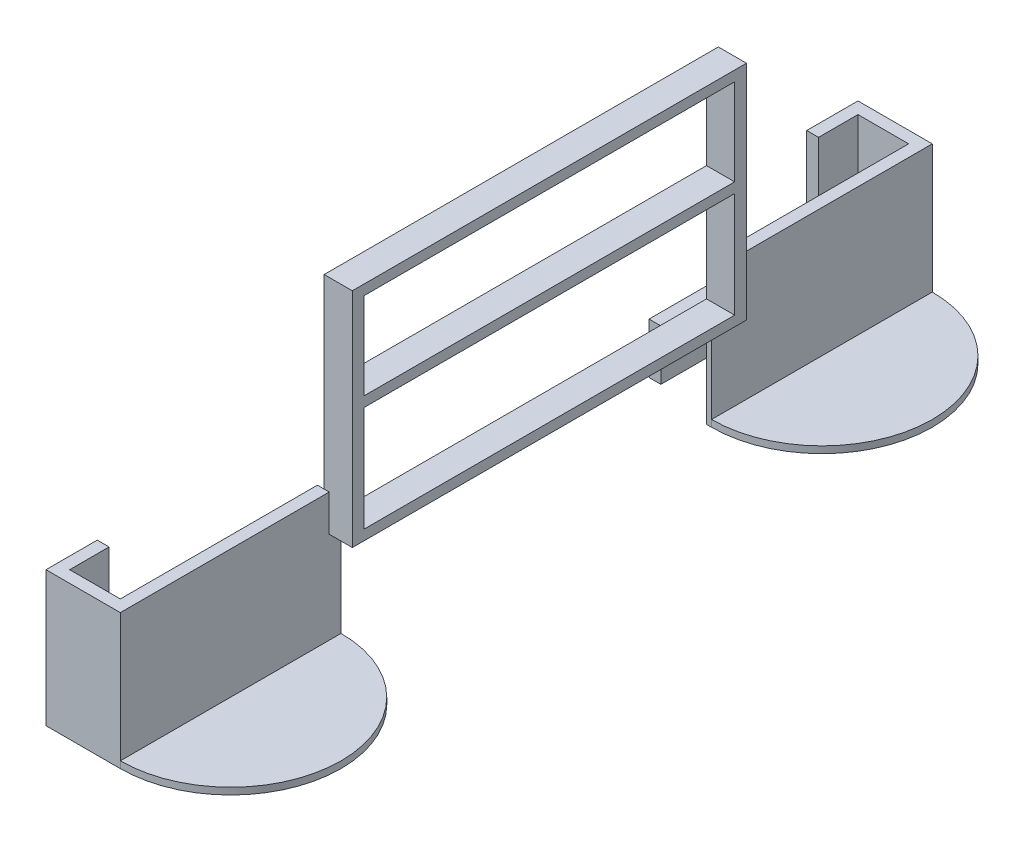
SolidWorks part; units mm, degrees
ref_plane "Alzado" through (0, 0, 0) normal (0, 0, 1) x (1, 0, 0)
ref_plane "Planta" through (0, 0, 0) normal (0, 1, 0) x (1, 0, 0)
ref_plane "Vista lateral" through (0, 0, 0) normal (1, 0, 0) x (0, 0, -1)
sketch "Croquis3" plane through (0, 0, 0) normal (0, 0, 1) x (1, 0, 0)
  line L0 (-207.2321, -11.9301) -> (-207.2321, -18.9301)
  line L1 (-207.2321, -11.9301) -> (-205.1321, -11.9301)
  line L2 (-205.1321, -11.9301) -> (-205.1321, -18.9301)
  line L3 (-205.1321, -18.9301) -> (-196.1321, -18.9301)
  line L4 (-196.1321, -18.9301) -> (-196.1321, -11.9301)
  line L5 (-196.1321, -11.9301) -> (-194.0321, -11.9301)
  line L6 (-194.0321, -11.9301) -> (-194.0321, -20.9301)
  line L7 (-194.0321, -20.9301) -> (-207.2321, -20.9301)
  line L8 (-207.2321, -20.9301) -> (-207.2321, -18.9301)
  dimension "D1" = 7
  dimension "D2" = 9
  dimension "D3" = 2.1
  dimension "D4" = 2.1
  dimension "D5" = 13.2
extrude "Saliente-Extruir2" add sketch "Croquis3" along normal blind 35
sketch "Croquis4" plane through (0, -18.9301, 0) normal (0, 1, 0) x (1, 0, 0)
  line L0 (-196.1321, -35) -> (-196.1321, 0) construction
  line L1 (-205.1321, 0) -> (-196.1321, 0)
  line L2 (-205.1321, 0) -> (-205.1321, -15)
  line L3 (-205.1321, -15) -> (-196.1321, -15)
  line L4 (-196.1321, 0) -> (-196.1321, -15)
  dimension "D1" = 15
extrude "Cortar-Extruir1" cut sketch "Croquis4" against normal blind 70
sketch "Croquis7" plane through (0, 0, 35) normal (0, 0, 1) x (1, 0, 0)
  line L0 (-205.1321, -11.9301) -> (-205.1321, 3.0699)
  line L1 (-205.1321, 3.0699) -> (-207.2321, 3.0699)
  line L2 (-207.2321, 3.0699) -> (-207.2321, -20.9301)
  line L3 (-207.2321, -20.9301) -> (-194.0321, -20.9301)
  line L4 (-194.0321, -20.9301) -> (-194.0321, 3.0699)
  line L5 (-194.0321, 3.0699) -> (-196.1321, 3.0699)
  line L9 (-196.1321, 3.0699) -> (-196.1321, -11.9301)
  line L10 (-196.1321, -11.9301) -> (-205.1321, -11.9301)
  dimension "D1" = 15
extrude "Saliente-Extruir3" add sketch "Croquis7" along normal blind 2.1
sketch "Croquis8" plane through (0, 0, 35) normal (0, 0, -1) x (-1, 0, 0)
  line L1 (194.0321, 3.0699) -> (196.1321, 3.0699)
  line L2 (194.0321, 3.0699) -> (194.0321, -11.9301)
  line L3 (194.0321, -11.9301) -> (196.1321, -11.9301)
  line L4 (196.1321, 3.0699) -> (196.1321, -11.9301)
  line L5 (205.1321, 3.0699) -> (207.2321, 3.0699)
  line L6 (205.1321, 3.0699) -> (205.1321, -11.9301)
  line L7 (205.1321, -11.9301) -> (207.2321, -11.9301)
  line L8 (207.2321, 3.0699) -> (207.2321, -11.9301)
extrude "Saliente-Extruir4" add sketch "Croquis8" along normal blind 7
sketch "Croquis9" plane through (-194.0321, 0, 0) normal (1, 0, 0) x (0, 0, -1)
  line L1 (-28, 3.0699) -> (0, 3.0699)
  line L2 (-28, 3.0699) -> (-28, -11.9301)
  line L3 (-28, -11.9301) -> (0, -11.9301)
  line L4 (0, 3.0699) -> (0, -11.9301)
extrude "Saliente-Extruir5" add sketch "Croquis9" against normal up to vertex
sketch "Croquis10" plane through (0, 0, 37.1) normal (0, 0, 1) x (1, 0, 0)
  line L1 (-205.1321, 3.0699) -> (-196.1321, 3.0699)
  line L2 (-205.1321, 3.0699) -> (-205.1321, -11.9301)
  line L3 (-205.1321, -11.9301) -> (-196.1321, -11.9301)
  line L4 (-196.1321, 3.0699) -> (-196.1321, -11.9301)
extrude "Saliente-Extruir6" add sketch "Croquis10" against normal up to vertex
sketch "Croquis11" plane through (-196.1321, 0, 0) normal (-1, 0, 0) x (0, 0, 1)
  line L0 (35, 3.0699) -> (35, -18.9301) construction
  line L2 (-35, -7.9301) -> (-35, -27.9301) construction
  dimension "D1" = 70
ref_plane "Plano1" through (0, 0, -35) normal (0, 0, -1) x (-1, 0, 0)
sketch "Croquis12" plane through (-194.0321, 0, 0) normal (1, 0, 0) x (0, 0, -1)
  line L0 (0, 3.0699) -> (0, 36.0699)
  line L1 (0, 36.0699) -> (35, 36.0699)
  line L2 (-37.1, -20.9301) -> (-37.1, 3.0699) construction
  line L3 (0, -20.9301) -> (2.1, -20.9301)
  line L4 (2.1, -20.9301) -> (2.1, -3.4301)
  line L5 (2.1, -3.4301) -> (35, -3.4301)
  line L6 (2.1, -1.6301) -> (35, -1.6301)
  line L7 (2.1, -1.6301) -> (2.1, 17.0699)
  line L8 (2.1, 17.0699) -> (35, 17.0699)
  line L9 (2.1, 18.8699) -> (35, 18.8699)
  line L10 (2.1, 18.8699) -> (2.1, 34.2699)
  line L11 (2.1, 34.2699) -> (35, 34.2699)
  line L12 (35, 36.0699) -> (35, 34.2699)
  line L13 (35, 18.8699) -> (35, 17.0699)
  line L14 (35, -1.6301) -> (35, -3.4301)
  line L15 (0, 3.0699) -> (0, -20.9301)
  dimension "D1" = 33
  dimension "D2" = 72.1
  dimension "D3" = 39.5
  dimension "D4" = 2.1
  dimension "D5" = 1.8
  dimension "D6" = 19
  dimension "D7" = 1.8
  dimension "D8" = 1.8
extrude "Saliente-Extruir7" add sketch "Croquis12" against normal blind 0.9
mirror "Simetría5" about plane through (0, 0, -35) normal (0, 0, -1) of bodies 112
sketch "Croquis13" plane through (0, -20.9301, 0) normal (0, -1, 0) x (1, 0, 0)
  line L2 (-194.0321, 37.1) -> (-194.0321, -2.1)
  line L3 (-194.0321, -67.9) -> (-194.0321, -107.1)
  arc A2 (-194.0321, 37.1) -> (-194.0321, -2.1) centre (-194.0321, 17.5) cw
  arc A3 (-194.0321, -67.9) -> (-194.0321, -107.1) centre (-194.0321, -87.5) cw
  dimension "D1" = 19.6
extrude "Saliente-Extruir8" add sketch "Croquis13" against normal blind 1.2
ref_plane "Plano2" through (-194.0321, 3.0699, 0) normal (0, -1, 0) x (-1, 0, 0)
sketch "Croquis16" plane through (-194.0321, 0, 0) normal (1, 0, 0) x (0, 0, -1)
  line L1 (0, 36.0699) -> (70, 36.0699)
  line L2 (0, 36.0699) -> (0, -3.4301)
  line L3 (0, -3.4301) -> (70, -3.4301)
  line L4 (70, 36.0699) -> (70, -3.4301)
  line L5 (2.1, 34.2699) -> (67.9, 34.2699)
  line L6 (2.1, 34.2699) -> (2.1, 18.8699)
  line L7 (2.1, 18.8699) -> (67.9, 18.8699)
  line L8 (67.9, 34.2699) -> (67.9, 18.8699)
  line L9 (2.1, 17.0699) -> (67.9, 17.0699)
  line L10 (2.1, 17.0699) -> (2.1, -1.6301)
  line L11 (2.1, -1.6301) -> (67.9, -1.6301)
  line L12 (67.9, 17.0699) -> (67.9, -1.6301)
extrude "Saliente-Extruir10" add sketch "Croquis16" along normal blind 4.1
